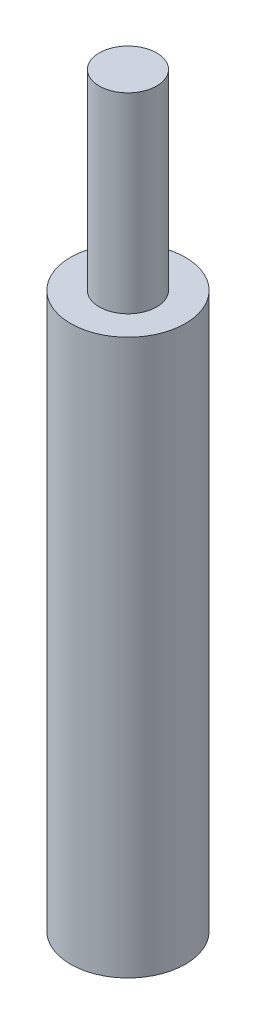
SolidWorks part; units mm, degrees
ref_plane "Front Plane" through (0, 0, 0) normal (0, 0, 1) x (1, 0, 0)
ref_plane "Top Plane" through (0, 0, 0) normal (0, 1, 0) x (1, 0, 0)
ref_plane "Right Plane" through (0, 0, 0) normal (1, 0, 0) x (0, 0, -1)
sketch "Sketch1" plane through (0, 0, 0) normal (0, 1, 0) x (1, 0, 0)
  circle A0 centre (0, 0) radius 3
  dimension "D1" = 6
extrude "Boss-Extrude1" add sketch "Sketch1" along normal blind 29
sketch "Sketch2" plane through (0, 29, 0) normal (0, 1, 0) x (1, 0, 0)
  circle A0 centre (0, 0) radius 1.5
  dimension "D1" = 3
extrude "Boss-Extrude2" add sketch "Sketch2" along normal blind 10
cosmetic thread "Cosmetic Thread1" parameters "D2"=2.439
hole_wizard "M3x0.5 Tapped Hole1" positions "Sketch4" profile "Sketch3" tap size "M3x0.5" standard "ANSI Metric"
sketch "Sketch4" plane through (0, 0, 0) normal (0, -1, 0) x (-1, 0, 0)
  point P0 (0, 0)
sketch "Sketch3" plane through (0, 0, 0) normal (1, 0, 0) x (0, 0, -1)
  line L0 (0, 0) -> (0, 5.7511)
  line L1 (0, 5.7511) -> (1.25, 5)
  line L2 (1.25, 5) -> (1.25, 0.275)
  line L3 (1.25, 0.275) -> (1.525, 0)
  line L5 (1.525, 0) -> (0, 0)
  line L6 (-1.25, 0.275) -> (-1.525, 0) construction
  line L10 (0, 5.7511) -> (-1.25, 5) construction
  line L11 (0, -6.35) -> (0, 107.95) construction
  dimension "Tap Drill Dia." = 2.5
  dimension "Tap Drill Depth" = 5
  dimension "Near C'Sink Dia." = 3.05
  dimension "Near C'Sink Angle" = 90
  dimension "Drill Angle" = 118
cosmetic thread "Hole Thread1" parameters "D1"=5, "D2"=3
